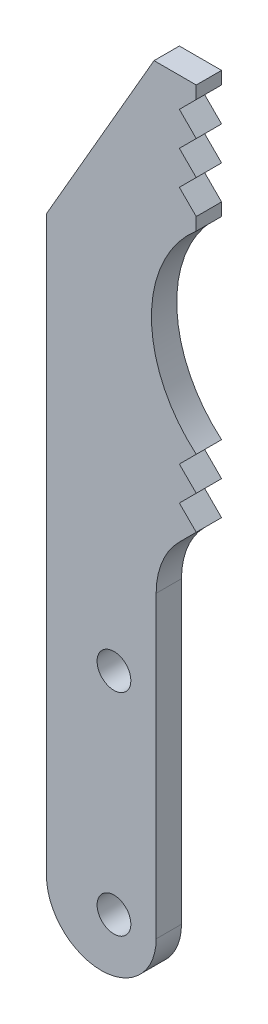
SolidWorks part; units mm, degrees
material "Balsa"
ref_plane "Front Plane" through (0, 0, 0) normal (0, 0, 1) x (1, 0, 0)
ref_plane "Top Plane" through (0, 0, 0) normal (0, 1, 0) x (1, 0, 0)
ref_plane "Right Plane" through (0, 0, 0) normal (1, 0, 0) x (0, 0, -1)
sketch "Sketch1" plane through (0, 0, 0) normal (0, 0, 1) x (1, 0, 0)
  line L0 (0, 0) -> (0, 90) construction
  line L1 (0, 90) -> (-5, 90) construction
  line L2 (-5, 90) -> (-17.75, 67.9164) construction
  line L3 (-17.75, 67.9164) -> (-17.75, 0) construction
  line L4 (-17.75, 0) -> (0, 0) construction
  line L5 (-2, 90) -> (-2, 75) construction
  line L6 (-2, 75) -> (0, 75) construction
  line L7 (0, 88.5) -> (-2, 86.5)
  line L8 (-2, 86.5) -> (0, 84.5)
  line L9 (0, 84.5) -> (-2, 82.5)
  line L10 (-2, 82.5) -> (0, 80.5)
  line L11 (0, 80.5) -> (-2, 78.5)
  line L12 (-2, 78.5) -> (0, 76.5)
  line L13 (-17.75, 64.3) -> (0, 64.3) construction
  line L14 (-9.75, 0) -> (-9.75, 25) construction
  line L15 (-2, 42.1) -> (0, 44.1)
  line L16 (0, 44.1) -> (-2, 46.1)
  line L17 (-2, 46.1) -> (0, 48.1)
  line L18 (0, 48.1) -> (-2, 50.1)
  line L19 (-2, 50.1) -> (0, 52.1)
  line L20 (0, 88.5) -> (0, 90)
  line L21 (0, 90) -> (-5, 90)
  line L22 (0, 76.5) -> (0, 75)
  line L23 (-5, 90) -> (-17.75, 67.9164)
  line L24 (-17.75, 67.9164) -> (-17.75, 0)
  line L25 (-4.75, 0) -> (-4.75, 35.4609)
  arc A0 (0, 75) -> (0, 52.1) centre (9.6901, 63.55) ccw
  arc A1 (-17.75, 0) -> (-4.75, 0) centre (-11.25, 0) ccw
  arc A2 (-2, 42.1) -> (-4.75, 35.4609) centre (4.6391, 35.4609) ccw
  circle A3 centre (-9.75, 0) radius 2
  circle A4 centre (-9.75, 25) radius 2
  dimension "D11" = 15
  dimension "D12" = 6.5
  dimension "D13" = 4
  dimension "D1" = 90
  dimension "D2" = 30
  dimension "D3" = 5
  dimension "D4" = 17.75
  dimension "D5" = 2
  dimension "D6" = 15
  dimension "D7" = 1.5
  dimension "D8" = 3.5
  dimension "D10" = 24.2
  dimension "D14" = 5
  dimension "D15" = 25
  dimension "D9" = 3
extrude "Boss-Extrude1" add sketch "Sketch1" along normal mid plane 3
sketch "Sketch2" plane through (0, 0, 0) normal (0, 0, 1) x (1, 0, 0)
  line L0 (-15, -8.4108) -> (-15, 23.5892)
  line L1 (-4.75, 0) -> (-4.75, 35.4609) construction
  line L2 (-4.75, 0) -> (-4.75, -8.4108)
  line L3 (-4.75, -8.4108) -> (-15, -8.4108)
  line L4 (-4.75, 0) -> (-4.75, 35.4609)
  arc A0 (-15, 23.5892) -> (-4.75, 35.4609) centre (-3, 23.5892) cw
  dimension "D2" = 12
  dimension "D1" = 10.25
  dimension "D3" = 32
extrude "Cut-Extrude1" [suppressed] cut sketch "Sketch2" against normal mid plane 5
sketch "Sketch3" plane through (0, 0, 1.5) normal (0, 0, 1) x (1, 0, 0)
  line L0 (-3.1276, 88.5) -> (-3.1276, 43.0931)
  line L34 (-2.1213, 88.5) -> (-4.134, 88.5)
  line L35 (-4.134, 88.5) -> (-16.25, 67.5144)
  line L36 (-16.25, 67.5144) -> (-16.25, 0)
  line L37 (-6.25, 0) -> (-6.25, 35.4609)
  line L38 (-3.0607, 43.1607) -> (-2.1213, 44.1)
  line L39 (-2.1213, 44.1) -> (-4.1213, 46.1)
  line L40 (-4.1213, 46.1) -> (-2.1213, 48.1)
  line L41 (-2.1213, 48.1) -> (-4.1213, 50.1)
  line L42 (-4.1213, 50.1) -> (-2.1565, 52.0648)
  line L43 (-1.5, 75.6757) -> (-1.5, 75.8787)
  line L44 (-1.5, 75.8787) -> (-4.1213, 78.5)
  line L45 (-4.1213, 78.5) -> (-2.1213, 80.5)
  line L46 (-2.1213, 80.5) -> (-4.1213, 82.5)
  line L47 (-4.1213, 82.5) -> (-2.1213, 84.5)
  line L48 (-2.1213, 84.5) -> (-4.1213, 86.5)
  line L49 (-4.1213, 86.5) -> (-2.1213, 88.5)
  line L50 (-2.1213, 88.5) -> (-4.134, 88.5)
  line L51 (-4.134, 88.5) -> (-16.25, 67.5144)
  line L52 (-16.25, 67.5144) -> (-16.25, 0)
  line L53 (-6.25, 0) -> (-6.25, 35.4609)
  line L54 (-3.0607, 43.1607) -> (-2.1213, 44.1) construction
  line L55 (-2.1213, 44.1) -> (-4.1213, 46.1) construction
  line L56 (-4.1213, 46.1) -> (-2.1213, 48.1) construction
  line L57 (-2.1213, 48.1) -> (-4.1213, 50.1) construction
  line L58 (-4.1213, 50.1) -> (-2.1565, 52.0648) construction
  line L59 (-1.5, 75.6757) -> (-1.5, 75.8787) construction
  line L60 (-1.5, 75.8787) -> (-4.1213, 78.5) construction
  line L61 (-4.1213, 78.5) -> (-2.1213, 80.5) construction
  line L62 (-2.1213, 80.5) -> (-4.1213, 82.5) construction
  line L63 (-4.1213, 82.5) -> (-2.1213, 84.5) construction
  line L64 (-2.1213, 84.5) -> (-4.1213, 86.5) construction
  line L65 (-4.1213, 86.5) -> (-2.1213, 88.5) construction
  arc A6 (-16.25, 0) -> (-6.25, 0) centre (-11.25, 0) ccw
  arc A7 (-3.0607, 43.1607) -> (-6.25, 35.4609) centre (4.6391, 35.4609) ccw
  arc A8 (-1.5, 75.6757) -> (-2.1565, 52.0648) centre (9.6901, 63.55) ccw
  arc A9 (-16.25, 0) -> (-6.25, 0) centre (-11.25, 0) ccw
  arc A10 (-3.0607, 43.1607) -> (-6.25, 35.4609) centre (4.6391, 35.4609) ccw
  arc A11 (-1.5, 75.6757) -> (-2.1565, 52.0648) centre (9.6901, 63.55) ccw
  circle M20 centre (-9.75, 0) radius 2
  circle M41 centre (-9.75, 25) radius 2
  dimension "D1" = 1.5
extrude "Cut-Extrude2" [suppressed] cut sketch "Sketch3" against normal blind 1 contours A11 L0 L50 L51 L52 A9 L53 A10 M41 M20
sketch "Sketch4" [suppressed] plane through (0, 0, 4) normal (0, 0, 1) x (1, 0, 0)
  circle A0 centre (-9.75, 25) radius 1.5 construction
  circle A1 centre (-9.75, 25) radius 1.5
  circle A2 centre (-9.75, 0) radius 1.5 construction
  circle A3 centre (-9.75, 0) radius 1.5
extrude "Extrude-Thin1" [suppressed] add sketch "Sketch4" along normal blind 1 thin
sketch "Sketch5" [suppressed] plane through (0, 0, 4) normal (0, 0, 1) x (1, 0, 0)
  line L6 (-3.1276, 53.1598) -> (-16.25, 53.1598)
  line L12 (-3.1276, 73.9402) -> (-3.1276, 88.5)
  line L13 (-3.1276, 88.5) -> (-4.134, 88.5)
  line L14 (-4.134, 88.5) -> (-16.25, 67.5144)
  line L15 (-16.25, 67.5144) -> (-16.25, 0)
  line L16 (-6.25, 0) -> (-6.25, 35.4609)
  line L17 (-3.1276, 43.0931) -> (-3.1276, 53.1598)
  line L18 (-3.1276, 73.9402) -> (-3.1276, 88.5)
  line L19 (-3.1276, 88.5) -> (-4.134, 88.5)
  line L20 (-4.134, 88.5) -> (-16.25, 67.5144)
  line L21 (-16.25, 67.5144) -> (-16.25, 0)
  line L22 (-6.25, 0) -> (-6.25, 35.4609) construction
  line L23 (-3.1276, 43.0931) -> (-3.1276, 53.1598) construction
  arc A6 (-3.1276, 73.9402) -> (-3.1276, 53.1598) centre (9.6901, 63.55) ccw
  arc A7 (-16.25, 0) -> (-6.25, 0) centre (-11.25, 0) ccw
  arc A8 (-3.1276, 43.0931) -> (-6.25, 35.4609) centre (4.6391, 35.4609) ccw
  arc A9 (-3.1276, 73.9402) -> (-3.1276, 53.1598) centre (9.6901, 63.55) ccw
  arc A10 (-16.25, 0) -> (-6.25, 0) centre (-11.25, 0) ccw construction
  arc A11 (-3.1276, 43.0931) -> (-6.25, 35.4609) centre (4.6391, 35.4609) ccw construction
  arc M11 (-3.1276, 53.1598) -> (-3.1276, 73.9402) centre (9.6901, 63.55) cw
  line M12 (-3.1276, 73.9402) -> (-3.1276, 88.5)
  line M13 (-3.1276, 88.5) -> (-4.134, 88.5)
  line M14 (-4.134, 88.5) -> (-16.25, 67.5144)
  line M15 (-16.25, 67.5144) -> (-16.25, 0)
  dimension "D1" = 0
extrude "Cut-Extrude3" [suppressed] cut sketch "Sketch5" against normal blind 2 contours L6 M11 M12 M13 M14 M15
sketch "Sketch7" [suppressed] plane through (0, 0, 5) normal (0, 0, 1) x (1, 0, 0)
  line L0 (-16.25, 53.1598) -> (-3.1276, 53.1598)
  line L1 (-16.25, 53.1598) -> (-6.8099, 63.55)
  line L2 (-6.8099, 63.55) -> (-16.25, 67.5144)
  line L3 (-16.25, 67.5144) -> (-3.1276, 73.9402)
  arc A0 (-3.1276, 73.9402) -> (-3.1276, 53.1598) centre (9.6901, 63.55) ccw construction
extrude "Extrude-Thin3" [suppressed] add sketch "Sketch7" against normal up to body thin
sketch "Sketch8" [suppressed] plane through (0, 0, 5) normal (0, 0, 1) x (1, 0, 0)
  line L0 (-3.5674, 74.8383) -> (-3.1276, 73.9402) construction
  line L1 (-3.5674, 74.8383) -> (-3.1276, 73.9402)
  line L2 (-3.5674, 74.8383) -> (-3.1276, 75.0536)
  line L3 (-15.3538, 69.0668) -> (-3.5674, 74.8383) construction
  line L4 (-3.1276, 88.5) -> (-3.1276, 73.9402) construction
  line L5 (-3.1276, 75.0536) -> (-3.1276, 73.9402)
extrude "Boss-Extrude2" [suppressed] add sketch "Sketch8" against normal up to surface (3 mm away)
mirror "Mirror2" [suppressed] about plane through (0, 0, 0) normal (0, 0, 1)
fillet "Fillet1" [suppressed] radius 3.5
fillet "Fillet2" [suppressed] radius 0.15
